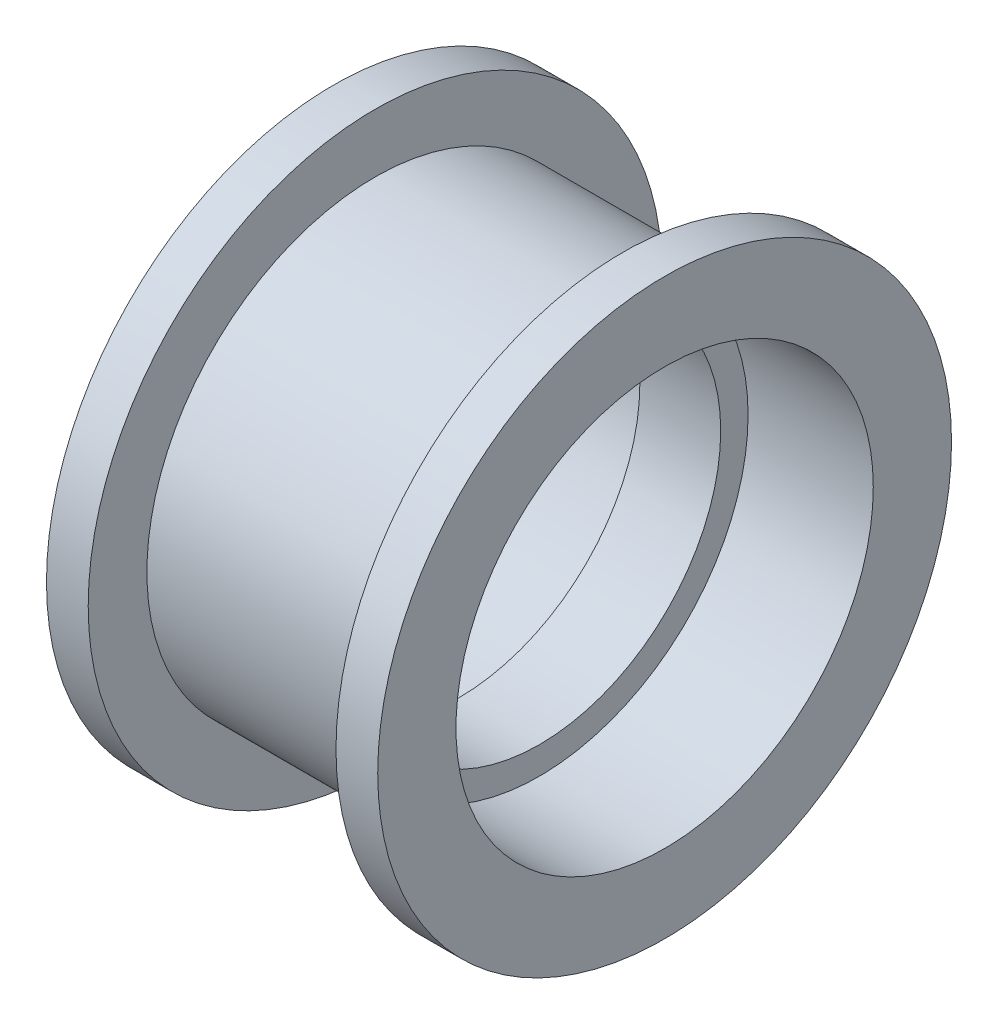
SolidWorks part; units mm, degrees
material "Delrin 2700 NC010, Low Viscosity Acetal Copolymer (SS)"
ref_plane "Front Plane" through (0, 0, 0) normal (0, 0, 1) x (1, 0, 0)
ref_plane "Top Plane" through (0, 0, 0) normal (0, 1, 0) x (1, 0, 0)
ref_plane "Right Plane" through (0, 0, 0) normal (1, 0, 0) x (0, 0, -1)
sketch "Sketch1" plane through (0, 0, 0) normal (0, 0, 1) x (1, 0, 0)
  line L0 (1.55, 6.95) -> (-1.55, 6.95)
  line L1 (-1.55, 6.95) -> (-1.55, 8)
  line L2 (-1.55, 8) -> (-6.35, 8)
  line L3 (-6.35, 8) -> (-6.35, 11)
  line L4 (-6.35, 11) -> (-4.75, 11)
  line L5 (-4.75, 8.75) -> (4.75, 8.75)
  line L6 (0, 8.75) -> (0, 6.95) construction
  line L7 (-4.75, 11) -> (-4.75, 8.75)
  line L8 (6.35, 8) -> (6.35, 11)
  line L9 (1.55, 8) -> (6.35, 8)
  line L10 (1.55, 6.95) -> (1.55, 8)
  line L11 (0, 0) -> (-12.6359, 0) construction
  line L12 (4.75, 11) -> (4.75, 8.75)
  line L13 (6.35, 11) -> (4.75, 11)
  dimension "D1" = 1.6
  dimension "8.64" = 13.9
  dimension "D2" = 16
  dimension "D3" = 17.5
  dimension "D4" = 3.1
  dimension "D5" = 22
  dimension "D6" = 12.7
revolve "Revolve1" add sketch "Sketch1" angle 360 about L11
ref_plane "Plane1" through (0, 0, 0) normal (1, 0, 0) x (0, 0, -1)
